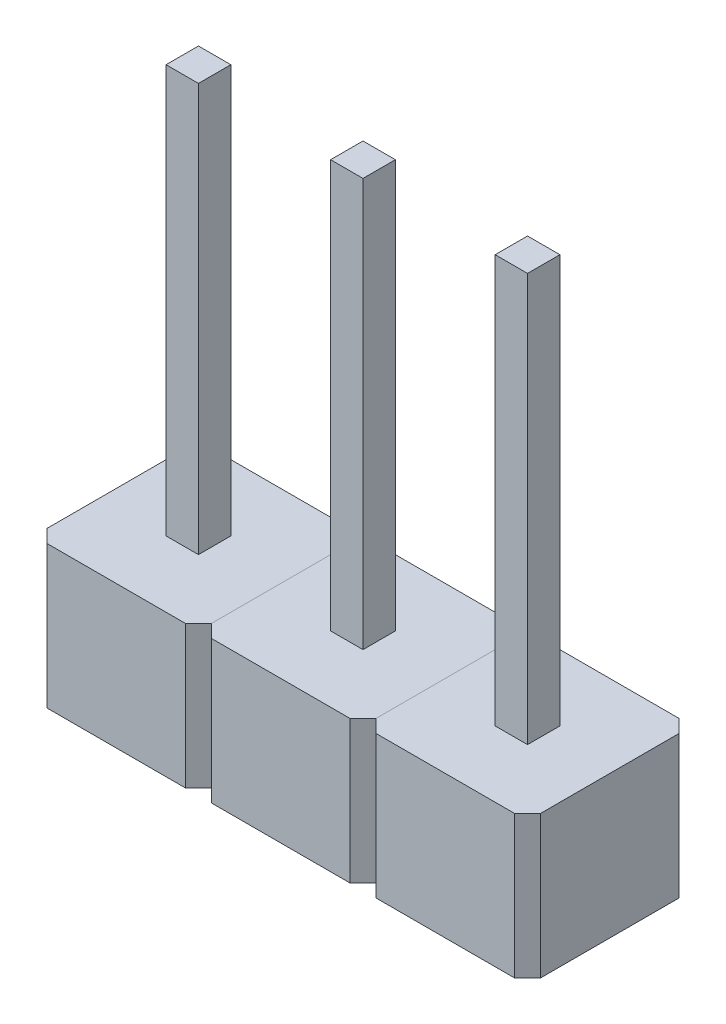
SolidWorks part; units mm, degrees
ref_plane "Alzado" through (0, 0, 0) normal (0, 0, 1) x (1, 0, 0)
ref_plane "Planta" through (0, 0, 0) normal (0, 1, 0) x (1, 0, 0)
ref_plane "Vista lateral" through (0, 0, 0) normal (1, 0, 0) x (0, 0, -1)
sketch "Croquis1" plane through (0, 0, 0) normal (0, 1, 0) x (1, 0, 0)
  line L0 (2.54, 0) -> (3.04, 0)
  line L1 (0, 0) -> (0.5, 0)
  line L2 (0, 0) -> (0, 0.5)
  line L3 (0, 0.5) -> (0.5, 0.5)
  line L4 (0.5, 0) -> (0.5, 0.5)
  line L5 (2.54, 0) -> (2.54, 0.5)
  line L6 (2.54, 0.5) -> (3.04, 0.5)
  line L7 (3.04, 0) -> (3.04, 0.5)
  line L8 (5.08, 0) -> (5.58, 0)
  line L9 (5.08, 0) -> (5.08, 0.5)
  line L10 (5.08, 0.5) -> (5.58, 0.5)
  line L11 (5.58, 0) -> (5.58, 0.5)
  dimension "D1" = 0.5
  dimension "D2" = 0.5
extrude "Extruir1" add sketch "Croquis1" along normal blind 8.5
sketch "Croquis2" plane through (0, 0, 0) normal (0, -1, 0) x (1, 0, 0)
  line L0 (0, 0) -> (0.5, 0) construction
  line L1 (-1.02, 1.02) -> (1.52, 1.02)
  line L2 (-1.02, 1.02) -> (-1.02, -1.52)
  line L3 (-1.02, -1.52) -> (1.52, -1.52)
  line L4 (1.52, 1.02) -> (1.52, -1.52)
  line L5 (0, -0.5) -> (0, 0) construction
  line L7 (0, 0) -> (0.5, 0)
  line L8 (0, 0) -> (0, -0.5)
  line L9 (0, -0.5) -> (0.5, -0.5)
  line L10 (0.5, 0) -> (0.5, -0.5)
  point P4 (0.25, 0)
  point P7 (0, -0.25)
  dimension "D1" = 2.54
  dimension "D2" = 2.54
  dimension "D3" = 1.27
  dimension "D4" = 1.27
extrude "Extruir2" add sketch "Croquis2" against normal blind 2.2 separate body
chamfer "Chaflán1" distance 0.2 angle 45 4 edges at (1.52, 1.1, -1.52) (1.52, 1.1, 1.02) (-1.02, 1.1, -1.52) (-1.02, 1.1, 1.02)
pattern_linear "MatrizL1" count 3 spacing 2.54 along (1, 0, 0) of bodies 106
